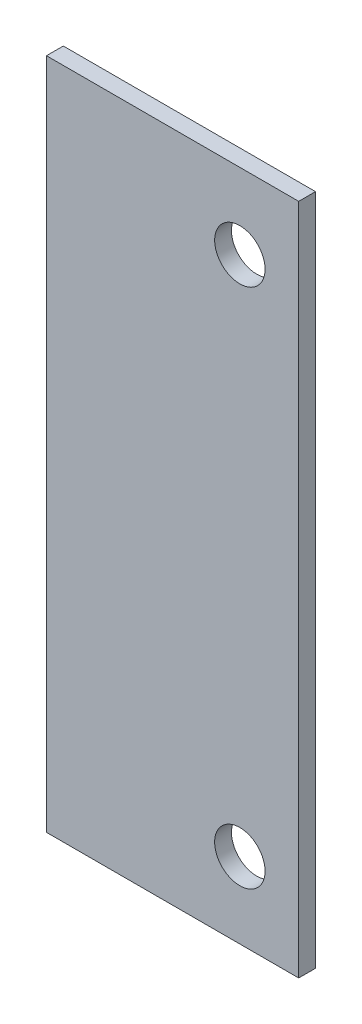
SolidWorks part; units mm, degrees
ref_plane "Płaszczyzna XY" through (0, 0, 0) normal (0, 0, 1) x (1, 0, 0)
ref_plane "Płaszczyzna XZ" through (0, 0, 0) normal (0, 1, 0) x (1, 0, 0)
ref_plane "Płaszczyzna YZ" through (0, 0, 0) normal (1, 0, 0) x (0, 0, -1)
sketch "Sketch1" plane through (0, 0, 0) normal (0, 0, 1) x (1, 0, 0)
  line L1 (-10, 40) -> (-10, -40)
  line L2 (-10, 40) -> (20, 40)
  line L3 (20, 40) -> (20, -40)
  line L4 (-10, -40) -> (20, -40)
  line L5 (-10, 40) -> (20, -40) construction
  line L6 (20, 40) -> (-10, -40) construction
  point P0 (5, 0)
  point P5 (5, 0)
  point P7 (0, 0)
  dimension "D1" = 80
  dimension "D2" = 30
  dimension "D3" = 20
extrude "Boss-Extrude1" add sketch "Sketch1" along normal blind 2
sketch "Sketch2" plane through (0, 0, 2) normal (0, 0, 1) x (1, 0, 0)
  circle A0 centre (13, 31) radius 3 construction
  circle A1 centre (13, -31) radius 3 construction
  circle A2 centre (13, 31) radius 3
  circle A3 centre (13, -31) radius 3
extrude "Cut-Extrude1" cut sketch "Sketch2" against normal blind 10
